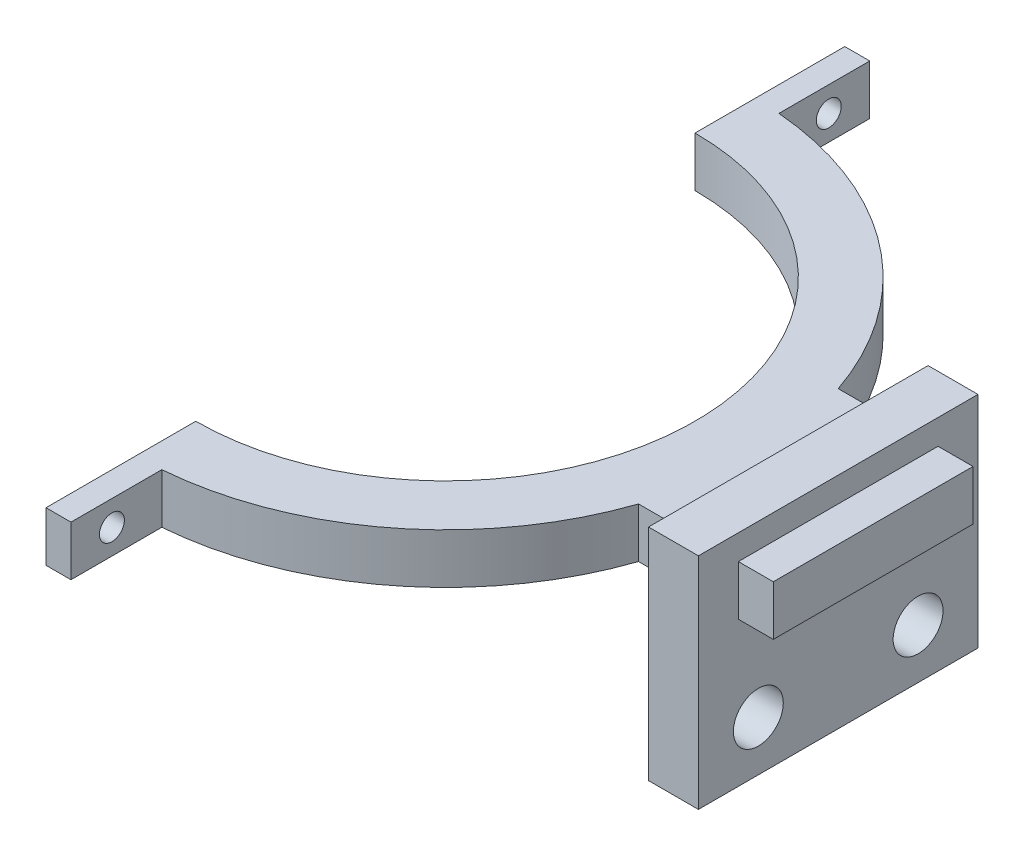
SolidWorks part; units mm, degrees
material "AISI Type 316L stainless steel"
ref_plane "Front Plane" through (0, 0, 0) normal (0, 0, 1) x (1, 0, 0)
ref_plane "Top Plane" through (0, 0, 0) normal (0, 1, 0) x (1, 0, 0)
ref_plane "Right Plane" through (0, 0, 0) normal (1, 0, 0) x (0, 0, -1)
sketch "Sketch1" plane through (0, 0, 0) normal (0, 1, 0) x (1, 0, 0)
  line L0 (0, -25) -> (0, -40)
  line L1 (0, -55) -> (0, 55) construction
  line L2 (0, -40) -> (2.5, -40)
  line L3 (2.5, -40) -> (2.5, -24.8747)
  line L4 (-55, 0) -> (55, 0) construction
  line L5 (2.5, 40) -> (2.5, 24.8747)
  line L6 (0, 40) -> (2.5, 40)
  line L7 (0, 25) -> (0, 40)
  line L8 (0, 0) -> (38.571, 0) construction
  line L9 (39.3428, 10) -> (29.3428, 10)
  line L10 (39.3428, -10) -> (29.3428, -10)
  line L11 (39.3428, 10) -> (39.3428, -10)
  circle A0 centre (0, 0) radius 25
  circle A1 centre (0, 0) radius 31
  point P22 (34.3428, 10)
  dimension "D1" = 50
  dimension "D2" = 6
  dimension "D3" = 15
  dimension "D4" = 2.5
  dimension "D5" = 20
  dimension "D6" = 10
extrude "Boss-Extrude1" add sketch "Sketch1" along normal blind 5
sketch "Sketch4" plane through (39.3428, 0, 0) normal (1, 0, 0) x (0, 0, -1)
  line L0 (0, -1.5751) -> (0, -16.3345) construction
  line L15 (0, 2.75) -> (0, -2.75) construction
  line L16 (-14, 7.5) -> (14, 7.5)
  line L18 (-14, 7.5) -> (-14, -14.5)
  line L19 (-14, -14.5) -> (14, -14.5)
  line L20 (14, 7.5) -> (14, -14.5)
  line L21 (-14, 7.5) -> (14, -14.5) construction
  line L22 (-14, -14.5) -> (14, 7.5) construction
  line L23 (10, 5) -> (-10, 5) construction
  circle A10 centre (8, -9.5) radius 2.5
  circle A11 centre (-8, -9.5) radius 2.5
  point P0 (0, -3.5)
  dimension "D3" = 22
  dimension "D6" = 8
  dimension "D4" = 5
  dimension "D1" = 2.5
  dimension "D2" = 28
  dimension "D5" = 5
extrude "Boss-Extrude3" add sketch "Sketch4" against normal blind 5
sketch "Sketch5" [suppressed] plane through (34.3428, 0, 0) normal (-1, 0, 0) x (0, 0, 1)
  circle A0 centre (-20, -7.7593) radius 5
  circle A1 centre (20, -7.7593) radius 5
  circle A2 centre (-8, -9.5) radius 4.365
  circle A3 centre (8, -9.5) radius 4.365
  dimension "D1" = 8.73
sketch "Sketch6" plane through (39.3428, 0, 0) normal (1, 0, 0) x (0, 0, -1)
  line L0 (0, 12.1) -> (0, -12.1) construction
  line L1 (-10, 5) -> (10, 5)
  line L2 (-10, 5) -> (-10, 0)
  line L3 (-10, 0) -> (10, 0)
  line L4 (10, 5) -> (10, 0)
  line L5 (-10, 5) -> (10, 0) construction
  line L6 (-10, 0) -> (10, 5) construction
  line L7 (-10, 5) -> (-30.899, 5) construction
  point P0 (0, 2.5)
  dimension "D1" = 2.5
  dimension "D2" = 5
  dimension "D3" = 20
extrude "Boss-Extrude4" add sketch "Sketch6" along normal blind 3.5
sketch "Sketch8" plane through (2.5, 0, 0) normal (1, 0, 0) x (0, 0, -1)
  line L0 (-40, 5) -> (-30.899, 5) construction
  line L1 (-30.899, 5) -> (-30.899, 0) construction
  line L2 (0, 12.1) -> (0, -12.1) construction
  circle A0 centre (-35.899, 2.5) radius 1.25
  circle A1 centre (35.899, 2.5) radius 1.25
  dimension "D1" = 2.5
  dimension "D2" = 2.5
  dimension "D3" = 5
extrude "Cut-Extrude1" cut sketch "Sketch8" against normal through all
